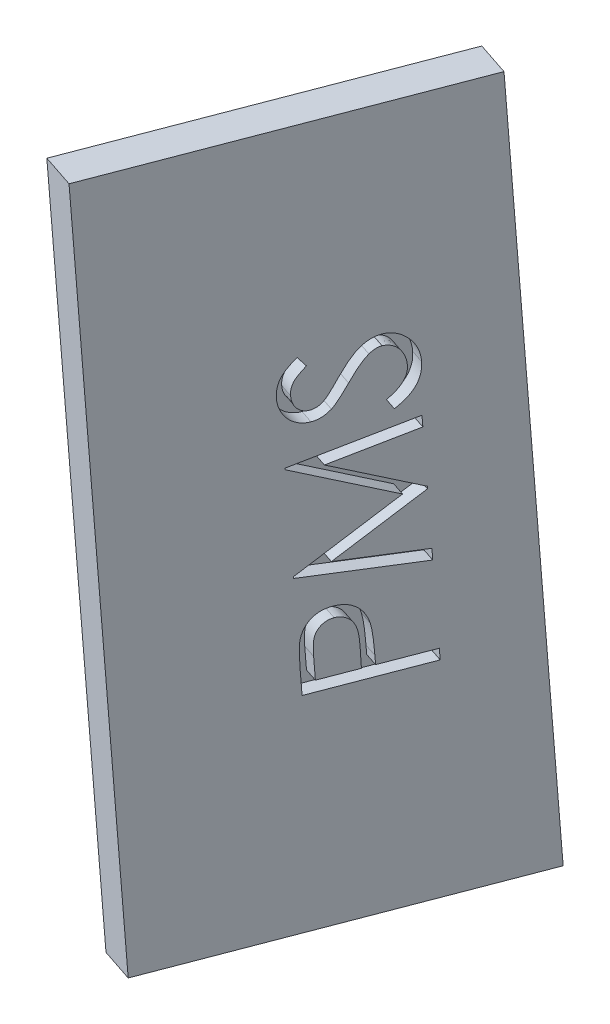
SolidWorks part; units mm, degrees
ref_plane "Front Plane" through (0, 0, 0) normal (0, 0, 1) x (1, 0, 0)
ref_plane "Top Plane" through (0, 0, 0) normal (0, 1, 0) x (1, 0, 0)
ref_plane "Right Plane" through (0, 0, 0) normal (1, 0, 0) x (0, 0, -1)
sketch "Sketch1" plane through (318.504, -806.1255, -1231.4628) normal (0.9163, 0.1171, 0.3829) x (0.1165, -0.9929, 0.025)
  line L1 (-54.6603, 256.2024) -> (-132.3603, 256.2024)
  line L2 (-54.6603, 256.2024) -> (-54.6603, 216.2024)
  line L3 (-54.6603, 216.2024) -> (-132.3603, 216.2024)
  line L4 (-132.3603, 256.2024) -> (-132.3603, 216.2024)
  dimension "D1" = 40
  dimension "D2" = 77.7
extrude "Boss-Extrude1" add sketch "Sketch1" along normal blind 5
sketch "Sketch3" plane through (-246.614, -31.5244, -103.0597) normal (0.9163, 0.1171, 0.3829) x (0.3831, 0.0217, -0.9234)
  line L0 (1488.1969, -752.0621) -> (1488.1969, -674.3621) construction
  line L1 (1457.9081, -752.0621) -> (1497.9081, -752.0621) construction
  line L2 (1497.9081, -674.3621) -> (1457.9081, -674.3621) construction
  text T0 "PMS" font "Century Gothic" height in points 48
extrude "Cut-Extrude2" cut sketch "Sketch3" against normal blind 2
